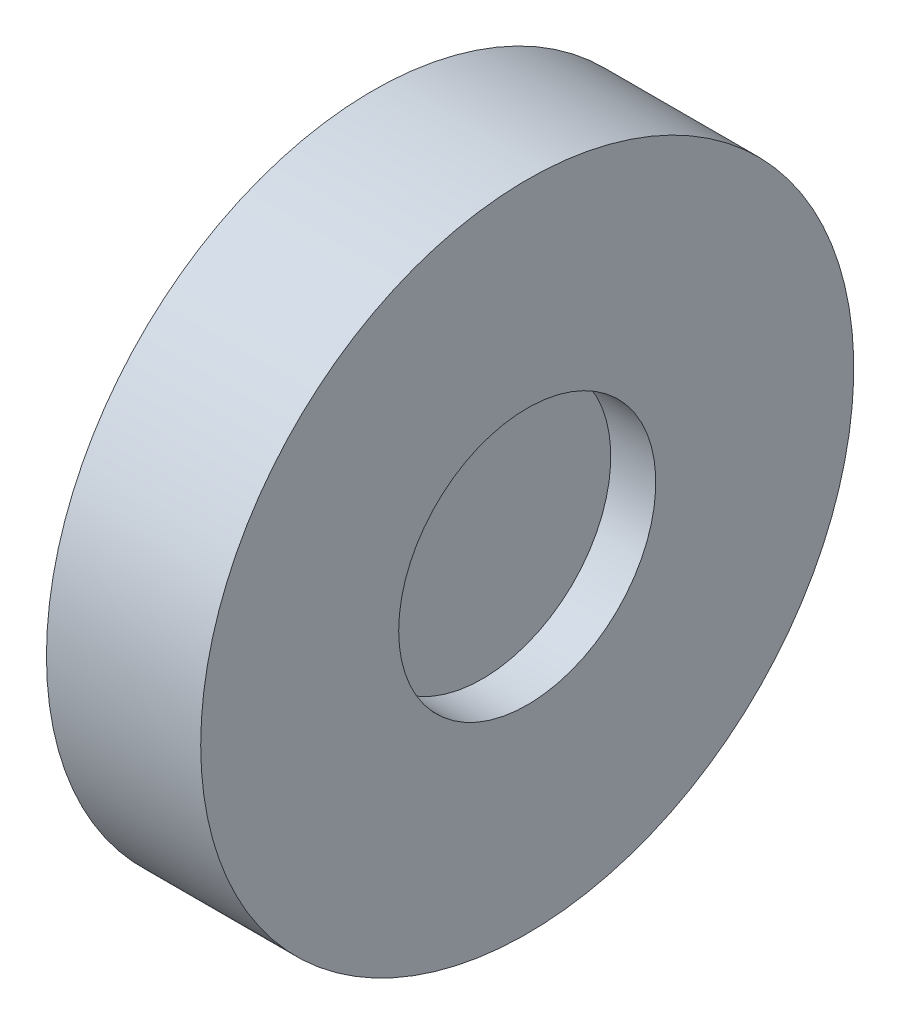
SolidWorks part; units mm, degrees
ref_plane "前视基准面" through (0, 0, 0) normal (0, 0, 1) x (1, 0, 0)
ref_plane "上视基准面" through (0, 0, 0) normal (0, 1, 0) x (1, 0, 0)
ref_plane "右视基准面" through (0, 0, 0) normal (1, 0, 0) x (0, 0, -1)
sketch "草图1" plane through (0, 0, 0) normal (0, 0, 1) x (1, 0, 0)
  line L0 (-1.25, 5) -> (-1.25, 0)
  line L2 (-1.25, 5) -> (1.25, 5)
  line L3 (-1.25, 0) -> (1.25, 0)
  line L4 (1.25, 5) -> (1.25, 0)
revolve "旋转2" add sketch "草图1" angle 360 about L3
sketch "草图4" plane through (0, 0, 0) normal (0, 0, 1) x (1, 0, 0)
  line L0 (-3, 12.7) -> (3, 12.7)
  line L1 (3, 12.7) -> (3, 5)
  line L2 (3, 5) -> (-3, 5)
  line L3 (1.25, 5) -> (-1.25, 5) construction
  line L4 (-3, 5) -> (-3, 12.7)
  line L5 (0, 5) -> (0, 12.7) construction
  line L6 (-1.6142, 0) -> (1.5903, 0) construction
revolve "旋转3" add sketch "草图4" angle 360 about L6
equation "\"D1@草图4\"=\"D1@草图1\""
